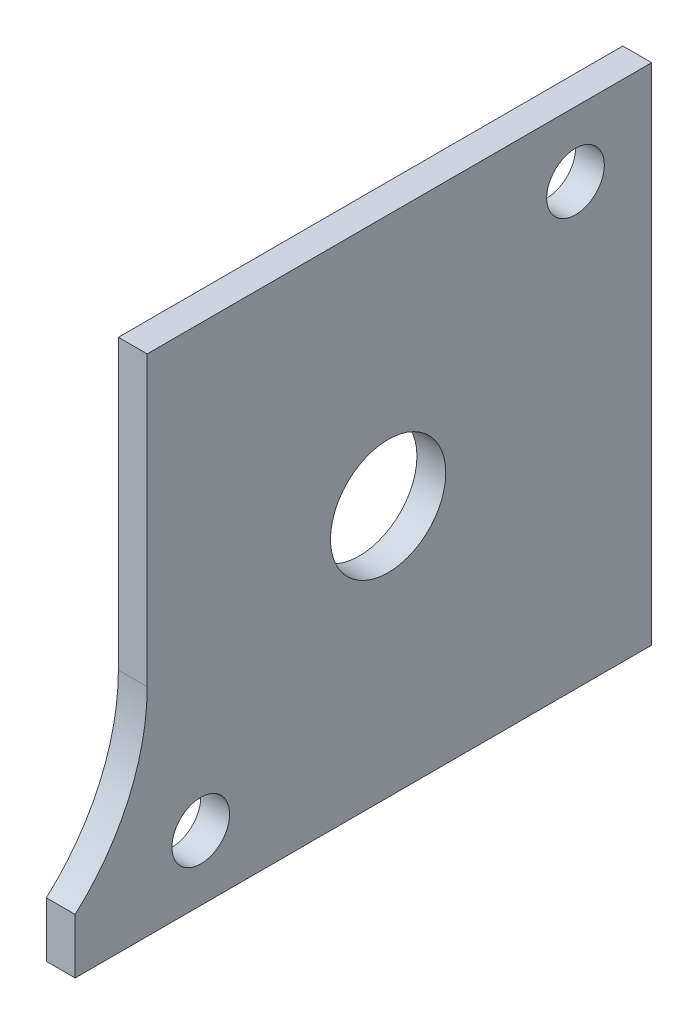
SolidWorks part; units mm, degrees
ref_plane "Front Plane" through (0, 0, 0) normal (0, 0, 1) x (1, 0, 0)
ref_plane "Top Plane" through (0, 0, 0) normal (0, 1, 0) x (1, 0, 0)
ref_plane "Right Plane" through (0, 0, 0) normal (1, 0, 0) x (0, 0, -1)
sketch "Sketch1" plane through (0, 0, 0) normal (1, 0, 0) x (0, 0, -1)
  line L1 (121.2969, -40.993) -> (121.2969, -5.993)
  line L2 (86.2969, -25.993) -> (86.2969, -5.993)
  line L3 (121.2969, -5.993) -> (86.2969, -5.993)
  line L4 (121.2969, -5.993) -> (102.0464, -5.993) construction
  line L5 (86.2969, -40.993) -> (86.2969, 1.007) construction
  line L6 (121.2969, -40.993) -> (81.2969, -40.993)
  line L7 (121.2969, -40.993) -> (102.0464, -40.993) construction
  line L9 (121.2969, -40.993) -> (121.2969, 1.007) construction
  line L10 (81.2969, -40.993) -> (81.2969, -37.1733)
  line L12 (81.2969, -25.993) -> (81.2969, -5.993) construction
  arc A0 (81.2969, -37.1733) -> (86.2969, -25.993) centre (71.2969, -25.993) ccw
  circle A2 centre (103.0114, -23.493) radius 4
  circle A8 centre (116.0114, -10.493) radius 2
  circle A10 centre (90.0114, -36.493) radius 2
extrude "Boss-Extrude1" add sketch "Sketch1" along normal blind 2
